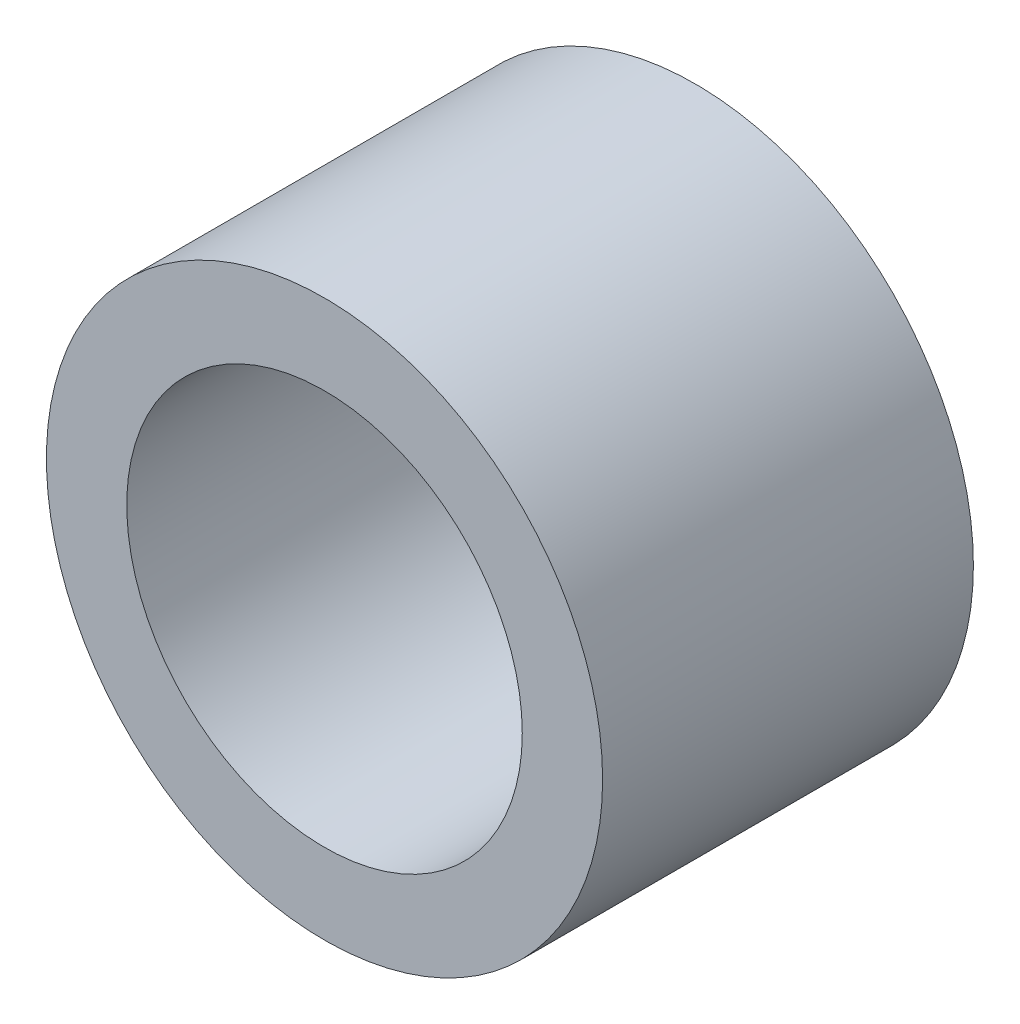
SolidWorks part; units mm, degrees
ref_plane "Front Plane" through (0, 0, 0) normal (0, 0, 1) x (1, 0, 0)
ref_plane "Top Plane" through (0, 0, 0) normal (0, 1, 0) x (1, 0, 0)
ref_plane "Right Plane" through (0, 0, 0) normal (1, 0, 0) x (0, 0, -1)
sketch "Sketch1" plane through (0, 0, 0) normal (0, 0, 1) x (1, 0, 0)
  line L0 (0, 1.6) -> (0, 2.25) construction
  line L1 (0, -1.6) -> (0, -2.25) construction
  circle A0 centre (0, 0) radius 2.25
  circle A1 centre (0, 0) radius 1.6
  dimension "OD" = 4.5
  dimension "ID" = 3.2
sketch "Sketch2" plane through (0, 0, 0) normal (1, 0, 0) x (0, 0, -1)
  line L0 (-1.5, 1.6) -> (1.5, 1.6) construction
  line L1 (-1.5, -1.6) -> (1.5, -1.6) construction
  line L2 (-1.5, -2.25) -> (1.5, -2.25) construction
  line L3 (-1.5, 2.25) -> (1.5, 2.25) construction
  dimension "Length" = 3
extrude "Extrude1" add sketch "Sketch1" along normal up to vertex (1.5 mm away) and the other way up to vertex (1.5 mm away) up to point (0, 1.6, 1.5) other way up to point (0, 1.6, -1.5)
sketch "Sketch3" plane through (0, 0, 1.5) normal (0, 0, 1) x (1, 0, 0)
  circle A0 centre (0, 0) radius 1.6 construction
  circle A3 centre (0, 0) radius 1.6
  point P3 (-1.6, 0)
